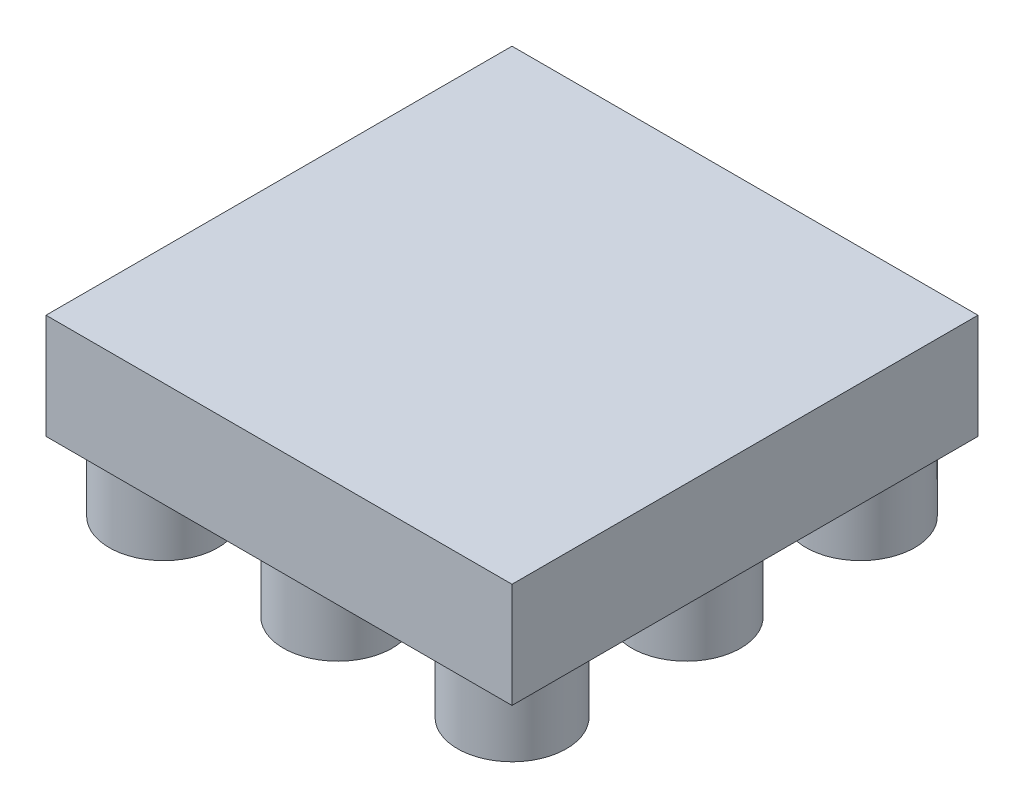
SolidWorks part; units mm, degrees
ref_plane "Front Plane" through (0, 0, 0) normal (0, 0, 1) x (1, 0, 0)
ref_plane "Top Plane" through (0, 0, 0) normal (0, 1, 0) x (1, 0, 0)
ref_plane "Right Plane" through (0, 0, 0) normal (1, 0, 0) x (0, 0, -1)
ref_plane "Plane2" through (0, 1.5875, 0) normal (0, 1, 0) x (-1, 0, 0)
sketch "Sketch3" plane through (0, 1.5875, 0) normal (0, 1, 0) x (-1, 0, 0)
  line L1 (-7.01, -15.61) -> (-17.71, -15.61)
  line L2 (-7.01, -15.61) -> (-7.01, -26.31)
  line L3 (-7.01, -26.31) -> (-17.71, -26.31)
  line L4 (-17.71, -15.61) -> (-17.71, -26.31)
extrude "Boss-Extrude2" add sketch "Sketch3" along normal blind 2.41
sketch "Sketch5" plane through (0, 1.5875, 0) normal (0, -1, 0) x (1, 0, 0)
  circle A0 centre (16.36, -24.96) radius 1.25
  circle A1 centre (12.36, -24.96) radius 1.25
  circle A2 centre (8.36, -24.96) radius 1.25
  circle A3 centre (16.36, -20.96) radius 1.25
  circle A4 centre (12.36, -20.96) radius 1.25
  circle A5 centre (8.36, -20.96) radius 1.25
  circle A6 centre (16.36, -16.96) radius 1.25
  circle A7 centre (12.36, -16.96) radius 1.25
  circle A8 centre (8.36, -16.96) radius 1.25
  dimension "D1" = 3
  dimension "D2" = 3
extrude "Boss-Extrude3" add sketch "Sketch5" along normal blind 1.5875
sketch "Sketch6" plane through (0, 3.9975, 0) normal (0, 1, 0) x (1, 0, 0)
  line L1 (-0.5, 15) -> (23.5, 15)
  line L2 (-0.5, 15) -> (-0.5, 26.5)
  line L3 (-0.5, 26.5) -> (23.5, 26.5)
  line L4 (23.5, 15) -> (23.5, 26.5)
extrude "Boss-Extrude4" [suppressed] add sketch "Sketch6" along normal blind 1.5875 separate body
sketch "Sketch7" plane through (17.71, 0, 0) normal (1, 0, 0) x (0, 0, -1)
  line L0 (15.61, 3.9975) -> (26.31, 3.9975) construction
  line L1 (15.61, 2.1895) -> (22.6914, 2.1895)
  line L2 (15.61, 2.1895) -> (15.61, 3.9975)
  line L3 (15.61, 3.9975) -> (22.6914, 3.9975)
  line L4 (22.6914, 2.1895) -> (22.6914, 3.9975)
  line L5 (15.61, 3.9975) -> (15.61, 1.5875) construction
extrude "Boss-Extrude5" [suppressed] add sketch "Sketch7" along normal blind 5.79 separate body
sketch "Sketch8" [suppressed] plane through (7.01, 0, 0) normal (-1, 0, 0) x (0, 0, 1)
  line L1 (-22.6914, 2.1895) -> (-15.61, 2.1895)
  line L2 (-22.6914, 2.1895) -> (-22.6914, 3.9975)
  line L3 (-22.6914, 3.9975) -> (-15.61, 3.9975)
  line L4 (-15.61, 2.1895) -> (-15.61, 3.9975)
extrude "Boss-Extrude6" [suppressed] add sketch "Sketch8" along normal blind 7.51 separate body
